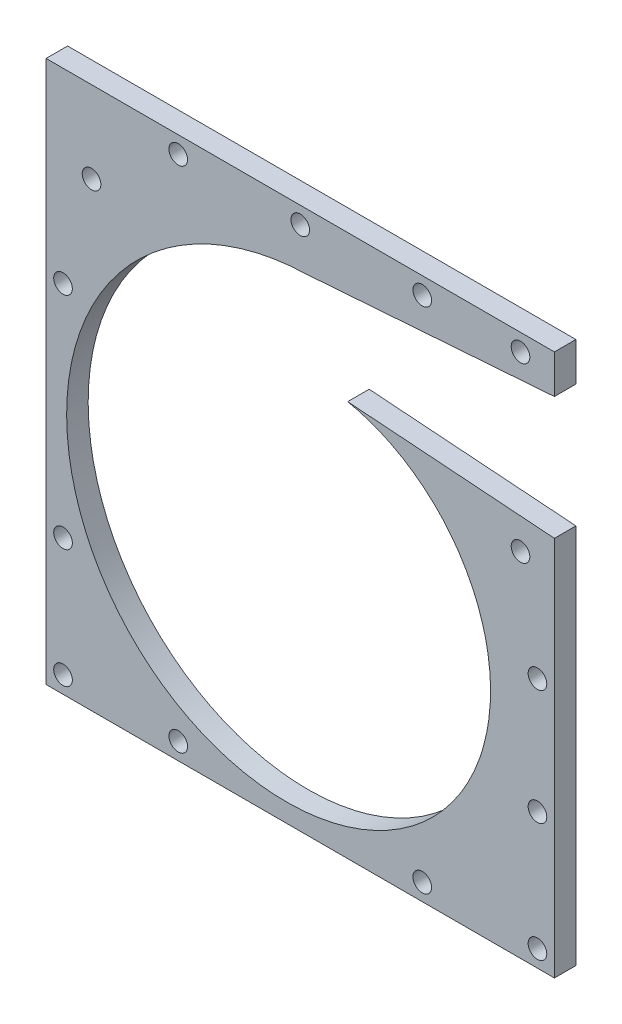
SolidWorks part; units mm, degrees
material "AISI 304"
ref_plane "Front Plane" through (0, 0, 0) normal (0, 0, 1) x (1, 0, 0)
ref_plane "Top Plane" through (0, 0, 0) normal (0, 1, 0) x (1, 0, 0)
ref_plane "Right Plane" through (0, 0, 0) normal (1, 0, 0) x (0, 0, -1)
sketch "Sketch1" plane through (0, 0, 0) normal (0, 0, 1) x (1, 0, 0)
  line L1 (-18.1818, -7.7823) -> (131.8182, -7.7823)
  line L2 (-18.1818, -7.7823) -> (-18.1818, 152.2177)
  line L3 (-18.1818, 152.2177) -> (131.8182, 152.2177)
  line L4 (131.8182, -7.7823) -> (131.8182, 152.2177)
  dimension "D1" = 160
  dimension "D2" = 150
extrude "Boss-Extrude1" add sketch "Sketch1" along normal blind 6.35
sketch "Sketch2" plane through (0, 0, 0) normal (0, 0, 1) x (1, 0, 0)
  line L0 (-18.1818, -7.7823) -> (131.8182, -7.7823) construction
  line L1 (56.8182, -7.7823) -> (56.8182, 152.2177) construction
  line L2 (131.8182, 152.2177) -> (-18.1818, 152.2177) construction
  line L3 (-18.1818, -7.7823) -> (131.8182, -7.7823) construction
  circle A0 centre (56.8182, 60.2177) radius 50 construction
  circle A1 centre (56.8182, 60.2177) radius 50
  point P0 (56.8182, 52.2686)
  dimension "D2" = 100
  dimension "D3" = 100
  dimension "D1" = 60.0509
  dimension "D4" = 68
extrude "Cut-Extrude2" cut sketch "Sketch2" along normal up to next
sketch "Sketch3" plane through (0, 0, 0) normal (0, 0, -1) x (-1, 0, 0)
  line L0 (-42.4775, -245.3976) -> (306.8559, -245.3976) construction
  line L1 (-107.6182, 60.2177) -> (-6.0182, 60.2177) construction
  circle A0 centre (-56.8182, 60.2177) radius 50.8 construction
  circle A2 centre (-56.8182, 60.2177) radius 50
  point P15 (-130.5969, 140.8094)
  dimension "D1" = 101.6
sketch "Sketch5" plane through (0, 0, 0) normal (0, 0, 1) x (1, 0, 0)
  circle A0 centre (56.8182, 60.2177) radius 50.75
  dimension "D1" = 101.5
curve "Helix/Spiral2"
sketch "Sketch8" plane through (0, 0, 6.35) normal (0, 0, 1) x (1, 0, 0)
  line L0 (58.9214, 135.5143) -> (131.8182, 140.8094)
  line L1 (131.8182, 140.8094) -> (131.8182, 104.5788)
  line L2 (131.8182, 104.5788) -> (70.8068, 109.0017)
  line L3 (131.8182, -7.7823) -> (131.8182, 152.2177) construction
  spline S0 degree 3 poles (1655.5435, -1075.034) (-228.3324, -143.7136) (-20.8405, 147.5337) (83.0512, 104.971) (85.9612, 103.445) (91.4793, 99.8417) (94.0872, 97.7644) (98.8965, 93.1188) (101.0976, 90.5506) (105.0006, 85.0032) (106.7023, 82.0242) (109.5297, 75.753) (110.6553, 72.461) (112.2729, 65.6758) (112.7649, 62.1828) (113.0797, 55.1183) (112.9026, 51.5469) (111.8674, 44.4542) (111.0093, 40.9331) (108.6254, 34.0713) (107.0996, 30.7308) (103.4181, 24.3573) (101.2626, 21.3244) (96.3841, 15.6851) (93.6612, 13.0788) (87.7328, 8.399) (84.5274, 6.3257) (77.7386, 2.801) (74.1554, 1.3498) (66.7323, -0.8617) (62.8926, -1.622) (55.0901, -2.4068) (51.1276, -2.4312) (43.2209, -1.7253) (39.277, -0.9949) (31.5517, 1.2125) (27.7706, 2.6894) (20.5125, 6.3541) (17.0358, 8.5417) (10.5204, 13.5651) (7.4819, 16.4007) (1.9637, 22.632) (-0.5158, 26.0275) (-4.8127, 33.2683) (-6.63, 37.1133) (-9.5212, 45.1235) (-10.5951, 49.2886) (-11.9436, 57.7947) (-12.2181, 62.1357) (-11.9401, 70.84) (-11.3874, 75.2031) (-9.4567, 83.7939) (-8.0786, 88.0214) (-4.5288, 96.1843) (-2.3571, 100.1197) (2.7183, 107.5494) (5.6219, 111.0435) (12.0718, 117.4547) (15.6179, 120.3715) (23.2377, 125.5099) (27.3113, 127.7313) (35.8497, 131.3839) (40.3143, 132.8149) (177.5509, 162.8074) (409.5643, -167.8845) (-1258.8776, -1322.0866) knots -1.018013 -1.018013 -1.018013 -1.018013 0.03125 0.03125 0.0625 0.0625 0.09375 0.09375 0.125 0.125 0.15625 0.15625 0.1875 0.1875 0.21875 0.21875 0.25 0.25 0.28125 0.28125 0.3125 0.3125 0.34375 0.34375 0.375 0.375 0.40625 0.40625 0.4375 0.4375 0.46875 0.46875 0.5 0.5 0.53125 0.53125 0.5625 0.5625 0.59375 0.59375 0.625 0.625 0.65625 0.65625 0.6875 0.6875 0.71875 0.71875 0.75 0.75 0.78125 0.78125 0.8125 0.8125 0.84375 0.84375 0.875 0.875 0.90625 0.90625 0.9375 0.9375 0.96875 0.96875 1.873185 1.873185 1.873185 1.873185 only from (70.8068, 109.0017) to (58.9214, 135.5143) construction
  spline S1 degree 3 poles (70.8068, 109.0017) (73.9425, 108.3689) (77.0418, 107.4329) (83.0512, 104.971) (85.9612, 103.445) (91.4793, 99.8417) (94.0872, 97.7644) (98.8965, 93.1188) (101.0976, 90.5506) (105.0006, 85.0032) (106.7023, 82.0242) (109.5297, 75.753) (110.6553, 72.461) (112.2729, 65.6758) (112.7649, 62.1828) (113.0797, 55.1183) (112.9026, 51.5469) (111.8674, 44.4542) (111.0093, 40.9331) (108.6254, 34.0713) (107.0996, 30.7308) (103.4181, 24.3573) (101.2626, 21.3244) (96.3841, 15.6851) (93.6612, 13.0788) (87.7328, 8.399) (84.5274, 6.3257) (77.7386, 2.801) (74.1554, 1.3498) (66.7323, -0.8617) (62.8926, -1.622) (55.0901, -2.4068) (51.1276, -2.4312) (43.2209, -1.7253) (39.277, -0.9949) (31.5517, 1.2125) (27.7706, 2.6894) (20.5125, 6.3541) (17.0358, 8.5417) (10.5204, 13.5651) (7.4819, 16.4007) (1.9637, 22.632) (-0.5158, 26.0275) (-4.8127, 33.2683) (-6.63, 37.1133) (-9.5212, 45.1235) (-10.5951, 49.2886) (-11.9436, 57.7947) (-12.2181, 62.1357) (-11.9401, 70.84) (-11.3874, 75.2031) (-9.4567, 83.7939) (-8.0786, 88.0214) (-4.5288, 96.1843) (-2.3571, 100.1197) (2.7183, 107.5494) (5.6219, 111.0435) (12.0718, 117.4547) (15.6179, 120.3715) (23.2377, 125.5099) (27.3113, 127.7313) (35.8497, 131.3839) (40.3143, 132.8149) (49.4812, 134.8183) (54.1832, 135.3906) (58.9214, 135.5143) knots 0 0 0 0 0.03125 0.03125 0.0625 0.0625 0.09375 0.09375 0.125 0.125 0.15625 0.15625 0.1875 0.1875 0.21875 0.21875 0.25 0.25 0.28125 0.28125 0.3125 0.3125 0.34375 0.34375 0.375 0.375 0.40625 0.40625 0.4375 0.4375 0.46875 0.46875 0.5 0.5 0.53125 0.53125 0.5625 0.5625 0.59375 0.59375 0.625 0.625 0.65625 0.65625 0.6875 0.6875 0.71875 0.71875 0.75 0.75 0.78125 0.78125 0.8125 0.8125 0.84375 0.84375 0.875 0.875 0.90625 0.90625 0.9375 0.9375 0.96875 0.96875 1 1 1 1
extrude "Cut-Extrude3" cut sketch "Sketch8" against normal up to next
sketch "Sketch9" plane through (0, 0, 6.35) normal (0, 0, 1) x (1, 0, 0)
  line L0 (131.8182, 140.8094) -> (131.8182, 152.2177) construction
  line L1 (126.8182, 152.2177) -> (126.8182, -7.7823) construction
  line L2 (131.8182, 152.2177) -> (-18.1818, 152.2177) construction
  line L3 (-18.1818, -7.7823) -> (131.8182, -7.7823) construction
  line L4 (131.8182, -7.7823) -> (131.8182, 104.5788) construction
  circle A1 centre (121.8182, 147.2177) radius 2.75
  circle A3 centre (92.8182, 147.2177) radius 2.75
  circle A5 centre (56.8182, 147.2177) radius 2.75
  circle A6 centre (20.8182, 147.2177) radius 2.75
  circle A7 centre (-4.7746, 128.0936) radius 2.75
  circle A8 centre (-13.1818, 97.2177) radius 2.75
  circle A9 centre (-13.1818, 32.2177) radius 2.75
  circle A10 centre (-13.1818, -2.7823) radius 2.75
  circle A11 centre (20.8182, -2.7823) radius 2.75
  circle A12 centre (92.8182, -2.7823) radius 2.75
  circle A13 centre (126.8182, -2.7823) radius 2.75
  circle A14 centre (126.8182, 32.2177) radius 2.75
  circle A15 centre (126.8182, 66.2177) radius 2.75
  circle A16 centre (121.8182, 96.2177) radius 2.75
  dimension "D11" = 10
  dimension "D2" = 29
  dimension "D3" = 36
  dimension "D4" = 31.9488
  dimension "D5" = 32
  dimension "D6" = 35
  dimension "D7" = 34
  dimension "D8" = 34
  dimension "D9" = 35
  dimension "D10" = 34
  dimension "D12" = 36
  dimension "D13" = 5
  dimension "D14" = 30
  dimension "D15" = 10
extrude "Cut-Extrude4" cut sketch "Sketch9" against normal up to next
